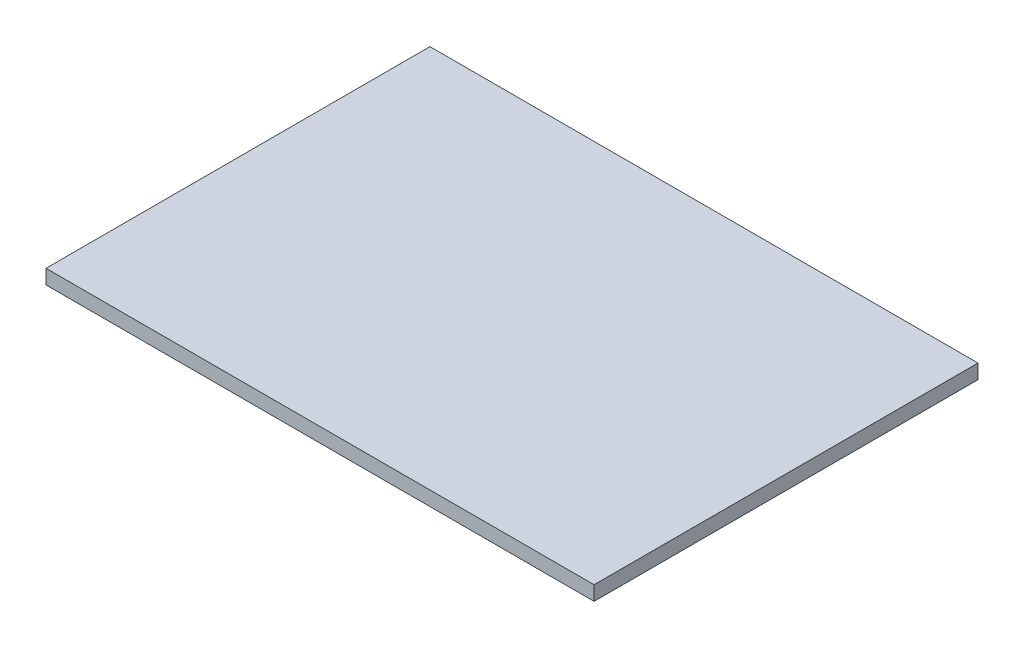
SolidWorks part; units mm, degrees
ref_plane "前视基准面" through (0, 0, 0) normal (0, 0, 1) x (1, 0, 0)
ref_plane "上视基准面" through (0, 0, 0) normal (0, 1, 0) x (1, 0, 0)
ref_plane "右视基准面" through (0, 0, 0) normal (1, 0, 0) x (0, 0, -1)
sketch "草图1" plane through (0, 0, 0) normal (0, 1, 0) x (1, 0, 0)
  line L0 (0, 0) -> (114, 0)
  line L1 (114, 0) -> (114, -79.8586)
  line L2 (114, -79.8586) -> (0, -79.8586)
  line L3 (0, -79.8586) -> (0, 0)
  dimension "D1" = 79.8586
  dimension "D2" = 114
extrude "凸台-拉伸1" add sketch "草图1" along normal blind 3
